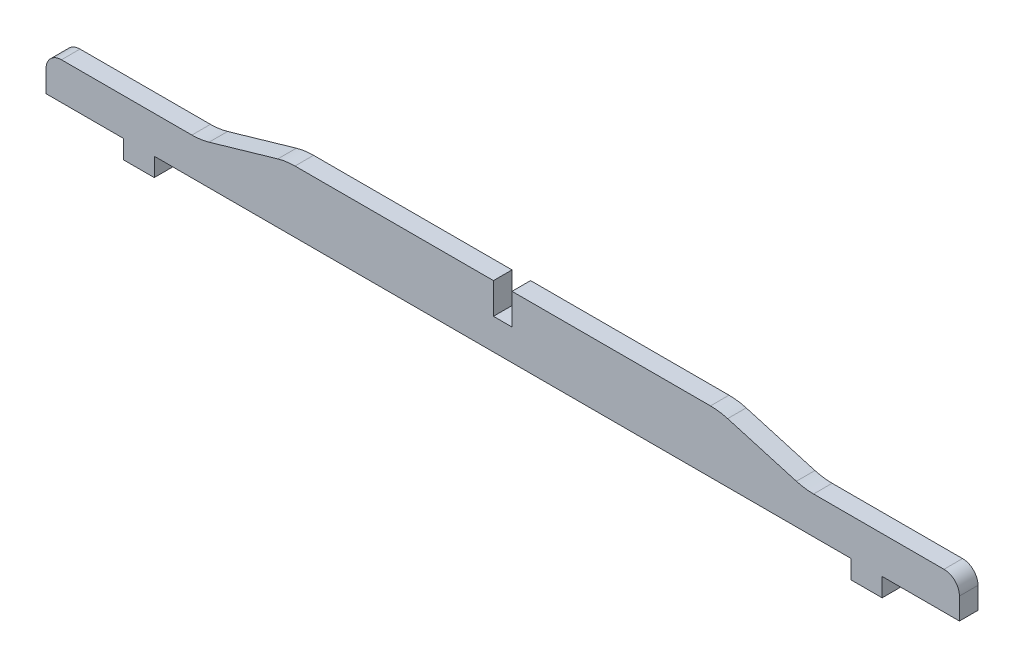
SolidWorks part; units mm, degrees
ref_plane "Front Plane" through (0, 0, 0) normal (0, 0, 1) x (1, 0, 0)
ref_plane "Top Plane" through (0, 0, 0) normal (0, 1, 0) x (1, 0, 0)
ref_plane "Right Plane" through (0, 0, 0) normal (1, 0, 0) x (0, 0, -1)
sketch "Sketch1" plane through (0, 0, 0) normal (0, 0, 1) x (1, 0, 0)
  line L0 (70, 0) -> (-70, 0)
  line L4 (112.6667, -20) -> (-112.6667, -20)
  line L5 (-147.6667, -20) -> (-122.6667, -20)
  line L6 (147.6667, -20) -> (122.6667, -20)
  line L7 (-122.6667, -20) -> (-122.6667, -26)
  line L8 (-122.6667, -26) -> (-112.6667, -26)
  line L9 (-112.6667, -26) -> (-112.6667, -20)
  line L10 (112.6667, -20) -> (112.6667, -26)
  line L11 (112.6667, -26) -> (122.6667, -26)
  line L12 (122.6667, -26) -> (122.6667, -20)
  line L13 (-147.6667, -20) -> (-147.6667, -8)
  line L14 (-147.6667, -8) -> (-97.6667, -8)
  line L15 (-97.6667, -8) -> (-70, 0)
  line L16 (70, 0) -> (97.6667, -8)
  line L17 (97.6667, -8) -> (147.6667, -8)
  line L18 (147.6667, -8) -> (147.6667, -20)
  point P4 (0, 0)
  point P10 (0, -20)
  dimension "D1" = 295.3333
  dimension "D2" = 20
  dimension "D3" = 6
  dimension "D4" = 10
  dimension "D7" = 12
  dimension "D5" = 50
  dimension "D6" = 140
  dimension "D8" = 25
extrude "Boss-Extrude1" add sketch "Sketch1" along normal blind 6
fillet "Fillet1" radius 5 2 edges at (147.6667, -8, 3) (-147.6667, -8, 3)
fillet "Fillet2" radius 20 4 edges at (97.6667, -8, 3) (70, 0, 3) (-70, 0, 3) (-97.6667, -8, 3)
sketch "Sketch2" plane through (0, 0, 6) normal (0, 0, 1) x (1, 0, 0)
  line L0 (0, 0) -> (0, -20) construction
  line L1 (67.1665, 0) -> (-67.1665, 0) construction
  line L2 (-112.6667, -20) -> (112.6667, -20) construction
  line L4 (-3, -10) -> (3, -10)
  line L5 (-3, -10) -> (-3, 0)
  line L6 (-3, 0) -> (3, 0)
  line L7 (3, -10) -> (3, 0)
  point P10 (0, 0)
  point P11 (0, 0)
  point P12 (0, 0)
  point P13 (0, -10)
  dimension "D1" = 6
extrude "Cut-Extrude1" cut sketch "Sketch2" against normal through all both and the other way through all
equation "\"D1@Sketch1\"=300-4.66666666"
